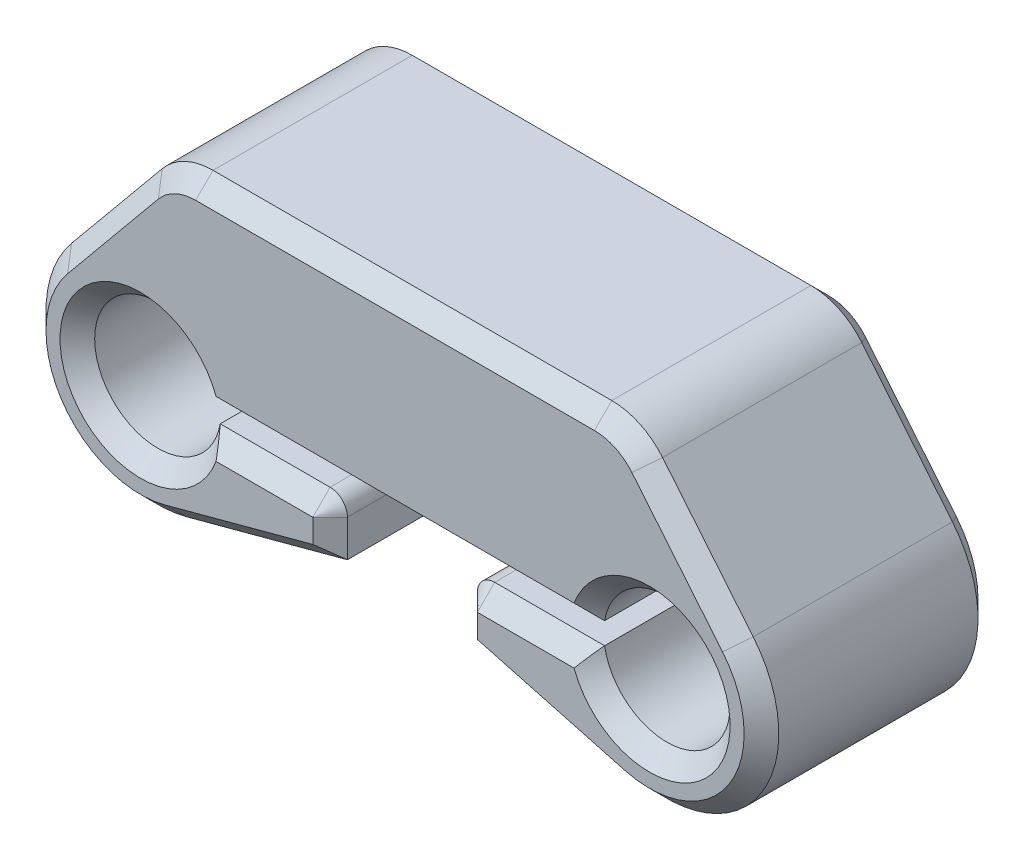
SolidWorks part; units mm, degrees
ref_plane "Front Plane" through (0, 0, 0) normal (0, 0, 1) x (1, 0, 0)
ref_plane "Top Plane" through (0, 0, 0) normal (0, 1, 0) x (1, 0, 0)
ref_plane "Right Plane" through (0, 0, 0) normal (1, 0, 0) x (0, 0, -1)
sketch "Sketch1" plane through (0, 0, 0) normal (0, 0, 1) x (1, 0, 0)
  line L0 (-37.3126, 0) -> (0, 0) construction
  line L1 (0, 0) -> (37.3126, 0) construction
  line L2 (0, 0) -> (0, -82.7752) construction
  circle A0 centre (-37.3126, 0) radius 12.7
  circle A1 centre (37.3126, 0) radius 12.7
  dimension "D1" = 25.4
  dimension "D2" = 74.6252
sketch "Sketch2" plane through (0, 0, 0) normal (0, 0, 1) x (1, 0, 0)
  line L0 (-29.2306, 30.0736) -> (29.2306, 30.0736)
  line L1 (36.6775, 26.5621) -> (49.9723, 10.4388)
  line L3 (-49.9723, 10.4388) -> (-36.6775, 26.5621)
  line L4 (0, 0) -> (0, 60.1472) construction
  line L5 (-86.3258, 0) -> (0, 0) construction
  line L6 (-28.1785, 1.5875) -> (28.1785, 1.5875)
  line L7 (-28.1785, -1.5875) -> (-12.065, -1.5875)
  line L8 (-9.525, -4.1275) -> (-9.525, -9.525)
  line L9 (9.525, -4.1275) -> (9.525, -9.525)
  line L10 (-9.525, -9.525) -> (-33.0554, -15.8465)
  line L11 (9.525, -9.525) -> (33.0554, -15.8465)
  line L12 (12.065, -1.5875) -> (28.1785, -1.5875)
  line L13 (46.5836, 0) -> (67.4629, 0) construction
  arc A0 (49.9723, 10.4388) -> (33.0554, -15.8465) centre (37.3126, 0) cw
  arc A4 (-49.9723, 10.4388) -> (-33.0554, -15.8465) centre (-37.3126, 0) ccw
  arc A5 (29.2306, 30.0736) -> (36.6775, 26.5621) centre (29.2306, 20.4216) cw
  arc A6 (-36.6775, 26.5621) -> (-29.2306, 30.0736) centre (-29.2306, 20.4216) cw
  arc A7 (-28.1785, 1.5875) -> (-28.1785, -1.5875) centre (-37.3126, 0) ccw
  arc A8 (28.1785, -1.5875) -> (28.1785, 1.5875) centre (37.3126, 0) ccw
  arc A9 (-12.065, -1.5875) -> (-9.525, -4.1275) centre (-12.065, -4.1275) cw
  arc A10 (9.525, -4.1275) -> (12.065, -1.5875) centre (12.065, -4.1275) cw
  point P18 (0, 30.0736)
  point P21 (33.782, 30.0736)
  point P24 (-33.782, 30.0736)
  point P35 (-9.525, -1.5875)
  point P38 (9.525, -1.5875)
  dimension "D1" = 107.442
  dimension "D3" = 67.564
  dimension "D2" = 2.54
  dimension "D4" = 9.652
  dimension "D5" = 18.542
  dimension "D9" = 46.482
  dimension "D12" = 36.6775
  dimension "D6" = 3.175
  dimension "D7" = 19.05
  dimension "D8" = 7.9375
  dimension "D10" = 30.0736
  dimension "D11" = 74.6252
extrude "Boss-Extrude2" add sketch "Sketch2" along normal blind 34.29
chamfer "Chamfer1" distance 2.54 angle 45 18 edges at (21.2902, -12.6858, 34.29) (9.525, -6.8263, 34.29) (10.2689, -2.3314, 34.29) (20.1218, -1.5875, 34.29) (46.5836, 0, 34.29) (0, 1.5875, 34.29) (-46.5836, 0, 34.29) (-20.1218, -1.5875, 34.29) (-10.2689, -2.3314, 34.29) (-9.525, -6.8263, 34.29) (-21.2902, -12.6858, 34.29) (-51.1104, -8.8801, 34.29) (-43.3249, 18.5004, 34.29) (-33.3473, 29.1517, 34.29) (0, 30.0736, 34.29) (33.3473, 29.1517, 34.29) (43.3249, 18.5004, 34.29) (51.1104, -8.8801, 34.29)
chamfer "Chamfer2" distance 2.54 angle 45 9 edges at (21.2902, -12.6858, 0) (-21.2902, -12.6858, 0) (51.1104, -8.8801, 0) (-51.1104, -8.8801, 0) (43.3249, 18.5004, 0) (-43.3249, 18.5004, 0) (33.3473, 29.1517, 0) (-33.3473, 29.1517, 0) (0, 30.0736, 0)
